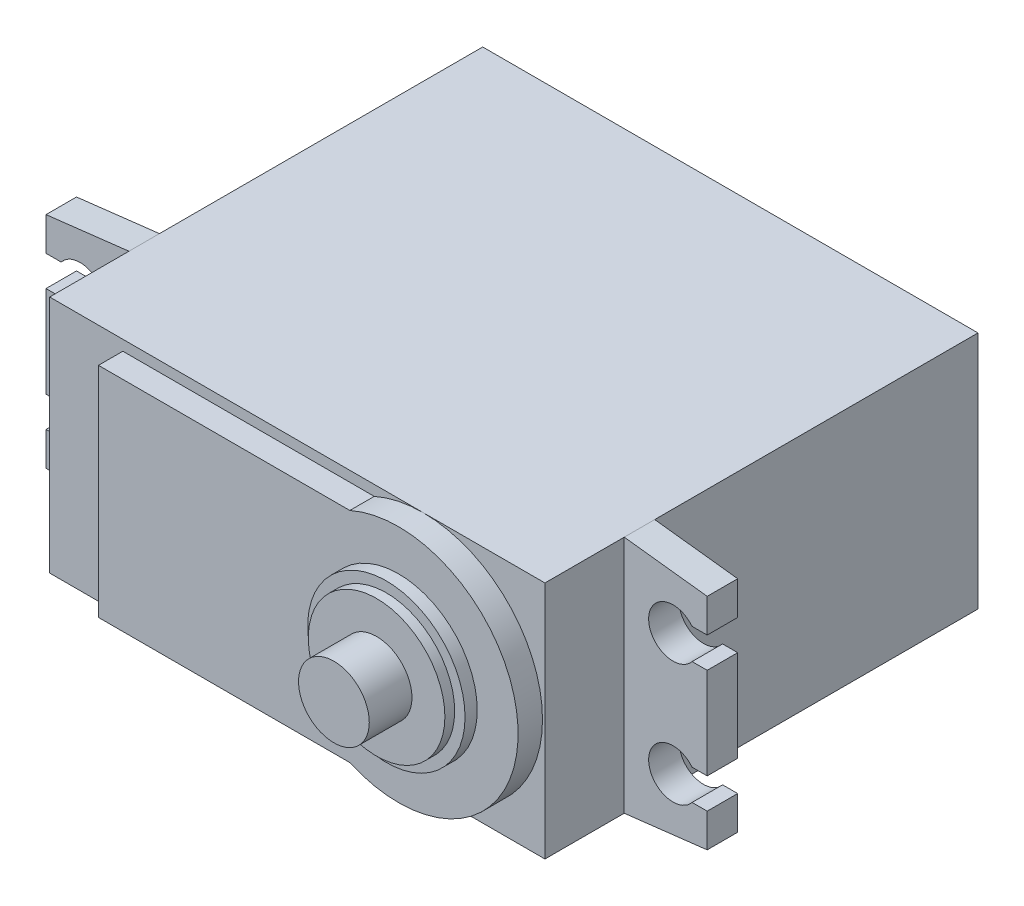
SolidWorks part; units mm, degrees
ref_plane "正面" through (0, 0, 0) normal (0, 0, 1) x (1, 0, 0)
ref_plane "平面" through (0, 0, 0) normal (0, 1, 0) x (1, 0, 0)
ref_plane "右側面" through (0, 0, 0) normal (1, 0, 0) x (0, 0, -1)
sketch "ｽｹｯﾁ1" plane through (0, 0, 0) normal (0, 0, 1) x (1, 0, 0)
  line L1 (0, 0) -> (40.6, 0)
  line L2 (0, 0) -> (0, 19.6)
  line L3 (0, 19.6) -> (40.6, 19.6)
  line L4 (40.6, 0) -> (40.6, 19.6)
  dimension "D1" = 40.6
  dimension "D2" = 19.6
extrude "ﾎﾞｽ - 押し出し1" add sketch "ｽｹｯﾁ1" along normal blind 35.5
sketch "ｽｹｯﾁ2" plane through (0, 0, 35.5) normal (0, 0, 1) x (1, 0, 0)
  line L0 (40.6, 9.8) -> (0, 9.8) construction
  line L1 (40.6, 0) -> (40.6, 19.6) construction
  line L2 (0, 19.6) -> (0, 0) construction
  line L3 (30.6, 0) -> (30.6, 19.6) construction
  line L4 (0, 0) -> (40.6, 0) construction
  line L5 (40.6, 19.6) -> (0, 19.6) construction
  circle A0 centre (30.6, 9.8) radius 9.8
  dimension "D2" = 19.6
  dimension "D1" = 10
extrude "ﾎﾞｽ - 押し出し2" add sketch "ｽｹｯﾁ2" along normal blind 2
sketch "ｽｹｯﾁ3" plane through (0, 0, 35.5) normal (0, 0, 1) x (1, 0, 0)
  line L0 (0, 9.8) -> (40.6, 9.8) construction
  line L1 (0, 19.6) -> (0, 0) construction
  line L2 (40.6, 0) -> (40.6, 19.6) construction
  line L3 (6, 0.85) -> (6, 18.75)
  line L4 (6, 18.75) -> (26.6078, 18.75)
  line L5 (6, 0.85) -> (26.6078, 0.85)
  line L6 (0, 0) -> (30.6, 0) construction
  line L7 (30.6, 18.75) -> (30.6, 0.85) construction
  line L8 (26.6078, 18.75) -> (26.6078, 0.85)
  arc A0 (30.6, 19.6) -> (30.6, 0) centre (30.6, 9.8) ccw construction
  point P9 (6, 9.8)
  dimension "D1" = 17.9
  dimension "D2" = 6
  dimension "D3" = 10
extrude "ﾎﾞｽ - 押し出し3" add sketch "ｽｹｯﾁ3" along normal blind 2
sketch "ｽｹｯﾁ4" plane through (0, 0, 37.5) normal (0, 0, 1) x (1, 0, 0)
  circle A0 centre (30.6, 9.8) radius 6.45
  dimension "D1" = 12.9
extrude "ﾎﾞｽ - 押し出し4" add sketch "ｽｹｯﾁ4" along normal blind 1
sketch "ｽｹｯﾁ5" plane through (0, 0, 38.5) normal (0, 0, 1) x (1, 0, 0)
  circle A0 centre (30.6, 9.8) radius 5.6
  dimension "D1" = 11.2
extrude "ﾎﾞｽ - 押し出し5" add sketch "ｽｹｯﾁ5" along normal blind 0.8
sketch "ｽｹｯﾁ7" plane through (0, 0, 39.3) normal (0, 0, 1) x (1, 0, 0)
  circle A0 centre (30.6, 9.8) radius 2.9
  dimension "D1" = 5.8
extrude "ﾎﾞｽ - 押し出し6" add sketch "ｽｹｯﾁ7" along normal blind 3.5
ref_plane "平面3" through (0, 0, 26.5) normal (0, 0, 1) x (1, 0, 0)
sketch "ｽｹｯﾁ8" plane through (0, 0, 26.5) normal (0, 0, 1) x (1, 0, 0)
  line L0 (0, 0) -> (-6.8, 0.8)
  line L1 (-6.8, 18.8) -> (-6.8, 0.8)
  line L2 (0, 0) -> (0, 19.6) construction
  line L3 (0, 19.6) -> (-6.8, 18.8)
  line L4 (0, 9.8) -> (40.6, 9.8) construction
  line L5 (0, 9.8) -> (-6.8, 9.8) construction
  line L6 (20.3, -3.8756) -> (20.3, 23.3977) construction
  line L7 (0, 19.6) -> (0, 0)
  line L8 (40.6, 19.6) -> (40.6, 0)
  line L9 (40.6, 19.6) -> (47.4, 18.8)
  line L10 (47.4, 18.8) -> (47.4, 0.8)
  line L11 (40.6, 0) -> (47.4, 0.8)
  point P12 (-6.8, 9.8)
  dimension "D1" = 18
  dimension "D2" = 19.6
  dimension "D3" = 6.8
  dimension "D4" = 40.6
extrude "ﾎﾞｽ - 押し出し7" add sketch "ｽｹｯﾁ8" along normal blind 2.5
sketch "ｽｹｯﾁ9" plane through (0, 0, 29) normal (0, 0, 1) x (1, 0, 0)
  line L0 (0, 9.8) -> (-6.8, 9.8) construction
  line L1 (0, 0) -> (0, 19.6) construction
  line L2 (-6.8, 18.8) -> (-6.8, 0.8) construction
  line L3 (-4, 3.0161) -> (-4, 17.5094) construction
  line L4 (0, 9.8) -> (40.6, 9.8) construction
  line L5 (20.3, 9.8) -> (20.3, -4.5394) construction
  line L6 (20.3, 9.8) -> (20.3, 23.5189) construction
  circle A0 centre (-4, 4.8) radius 2
  circle A1 centre (-4, 14.8) radius 2
  circle A2 centre (44.6, 14.8) radius 2
  circle A3 centre (44.6, 4.8) radius 2
  dimension "D2" = 4
  dimension "D3" = 4
  dimension "D1" = 4
  dimension "D4" = 5
  dimension "D5" = 5
  dimension "D6" = 40.6
extrude "ｶｯﾄ - 押し出し1" cut sketch "ｽｹｯﾁ9" against normal up to next
sketch "ｽｹｯﾁ10" plane through (0, 0, 29) normal (0, 0, 1) x (1, 0, 0)
  line L0 (-6.8, 18.8) -> (-6.8, 0.8) construction
  line L1 (-5.2, 6.05) -> (-6.8, 6.05)
  line L2 (-5.2, 6.05) -> (-5.2, 3.55)
  line L3 (-5.2, 3.55) -> (-6.8, 3.55)
  line L4 (-6.8, 6.05) -> (-6.8, 3.55)
  line L5 (-5.2, 6.05) -> (-6.8, 3.55) construction
  line L6 (-5.2, 3.55) -> (-6.8, 6.05) construction
  line L7 (-4, 4.8) -> (-6, 4.8) construction
  line L8 (-5.2, 16.05) -> (-6.8, 16.05)
  line L9 (-5.2, 16.05) -> (-5.2, 13.55)
  line L10 (-5.2, 13.55) -> (-6.8, 13.55)
  line L11 (-6.8, 16.05) -> (-6.8, 13.55)
  line L12 (-5.2, 16.05) -> (-6.8, 13.55) construction
  line L13 (-5.2, 13.55) -> (-6.8, 16.05) construction
  line L14 (-6, 4.8) -> (-6, 14.8) construction
  line L15 (-6, 14.8) -> (-4, 14.8) construction
  line L16 (0, 9.8) -> (40.6, 9.8) construction
  line L17 (0, 0) -> (0, 19.6) construction
  line L18 (20.3, 9.8) -> (20.3, -3.6113) construction
  line L19 (45.8, 16.05) -> (47.4, 16.05)
  line L20 (47.4, 16.05) -> (47.4, 13.55)
  line L21 (45.8, 13.55) -> (47.4, 13.55)
  line L22 (45.8, 16.05) -> (45.8, 13.55)
  line L23 (45.8, 6.05) -> (47.4, 6.05)
  line L24 (47.4, 6.05) -> (47.4, 3.55)
  line L25 (45.8, 3.55) -> (47.4, 3.55)
  line L26 (45.8, 6.05) -> (45.8, 3.55)
  circle A0 centre (-4, 4.8) radius 2 construction
  circle A1 centre (-4, 14.8) radius 2 construction
  point P0 (-6, 4.8)
  point P9 (-6, 14.8)
  dimension "D1" = 2.5
  dimension "D2" = 2.5
  dimension "D3" = 40.6
extrude "ｶｯﾄ - 押し出し2" cut sketch "ｽｹｯﾁ10" against normal up to next
